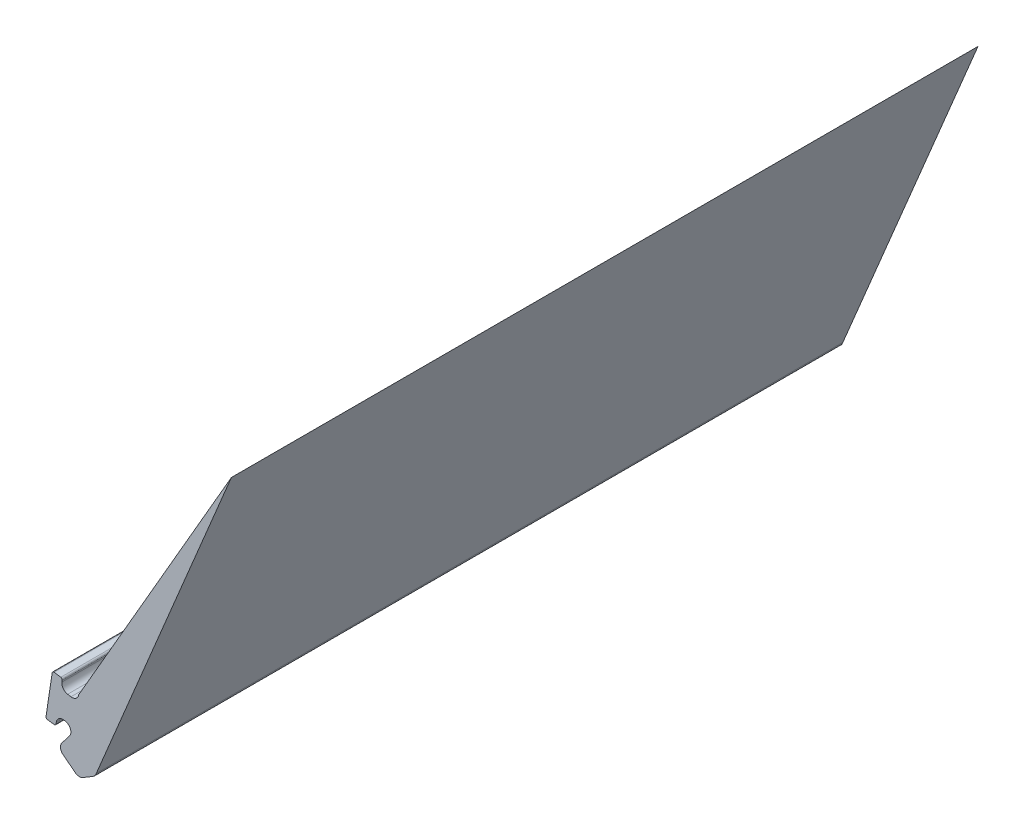
SolidWorks part; units mm, degrees
ref_plane "Front Plane" through (0, 0, 0) normal (0, 0, 1) x (1, 0, 0)
ref_plane "Top Plane" through (0, 0, 0) normal (0, 1, 0) x (1, 0, 0)
ref_plane "Right Plane" through (0, 0, 0) normal (1, 0, 0) x (0, 0, -1)
sketch "Sketch1" plane through (0, 0, 0) normal (0, 0, 1) x (1, 0, 0)
  line L13 (-21.3521, 11.1155) -> (-17.3688, 20.6615)
  line L18 (-17.3688, 20.6615) -> (-21.8688, 12.8672)
  line L19 (-22.0979, 12.7003) -> (-22.1962, 12.7159)
  line L20 (-22.3623, 12.9448) -> (-22.3547, 12.993)
  line L21 (-22.3966, 13.0503) -> (-22.593, 13.0799)
  line L22 (-22.6499, 13.0379) -> (-22.8321, 11.8292)
  line L23 (-22.7896, 11.7723) -> (-22.5924, 11.7444)
  line L24 (-22.5359, 11.7869) -> (-22.5295, 11.8322)
  line L25 (-22.2953, 12.0009) -> (-22.264, 11.9951)
  line L26 (-22.142, 11.6762) -> (-22.3655, 11.3868)
  line L32 (-22.3294, 11.1063) -> (-21.9695, 10.8283)
  line L33 (-21.744, 10.8153) -> (-21.4415, 10.9977)
  arc A16 (-21.8688, 12.8672) -> (-22.0979, 12.7003) centre (-22.0665, 12.8978) cw
  arc A17 (-22.1962, 12.7159) -> (-22.3623, 12.9448) centre (-22.1648, 12.9134) cw
  arc A18 (-22.5924, 11.7444) -> (-22.5359, 11.7869) centre (-22.5854, 11.7939) ccw
  arc A19 (-22.8321, 11.8292) -> (-22.7896, 11.7723) centre (-22.7826, 11.8218) ccw
  arc A20 (-22.593, 13.0799) -> (-22.6499, 13.0379) centre (-22.6004, 13.0304) ccw
  arc A21 (-22.3547, 12.993) -> (-22.3966, 13.0503) centre (-22.4041, 13.0009) ccw
  arc A22 (-22.5295, 11.8322) -> (-22.2953, 12.0009) centre (-22.3315, 11.8042) cw
  arc A23 (-22.264, 11.9951) -> (-22.142, 11.6762) centre (-22.3003, 11.7985) cw
  arc A24 (-21.4415, 10.9977) -> (-21.3521, 11.1155) centre (-21.5448, 11.169) ccw
  arc A25 (-21.9695, 10.8283) -> (-21.744, 10.8153) centre (-21.8472, 10.9866) ccw
  arc A26 (-22.3655, 11.3868) -> (-22.3294, 11.1063) centre (-22.2072, 11.2646) ccw
  dimension "D3" = 0.05
  dimension "D4" = 0.2
extrude "Boss-Extrude1" add sketch "Sketch1" against normal blind 22
